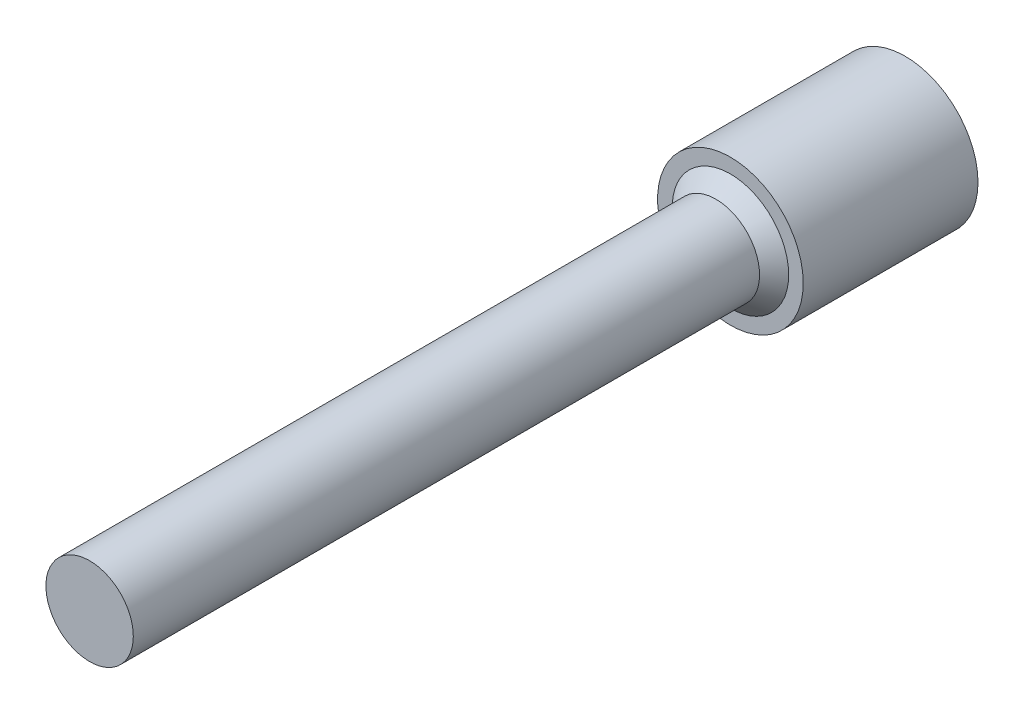
SolidWorks part; units mm, degrees
ref_plane "Front Plane" through (0, 0, 0) normal (0, 0, 1) x (1, 0, 0)
ref_plane "Top Plane" through (0, 0, 0) normal (0, 1, 0) x (1, 0, 0)
ref_plane "Right Plane" through (0, 0, 0) normal (1, 0, 0) x (0, 0, -1)
sketch "Sketch1" plane through (0, 0, 0) normal (0, 0, 1) x (1, 0, 0)
  circle A0 centre (0, 0) radius 2.5
  dimension "D1" = 5
extrude "Boss-Extrude1" add sketch "Sketch1" along normal blind 6
sketch "Sketch2" plane through (0, 0, 6) normal (0, 0, 1) x (1, 0, 0)
  circle A0 centre (0, 0) radius 1.5
  dimension "D1" = 3
extrude "Boss-Extrude2" add sketch "Sketch2" along normal blind 22
sketch "Sketch3" plane through (0, 0, 0) normal (0, 0, -1) x (-1, 0, 0)
  line L0 (0, 1) -> (0, -1) construction
  line L6 (0, 1) -> (-0.866, 0.5)
  line L7 (-0.866, 0.5) -> (-0.866, -0.5)
  line L8 (-0.866, -0.5) -> (0, -1)
  line L9 (0, -1) -> (0.866, -0.5)
  line L10 (0.866, -0.5) -> (0.866, 0.5)
  line L11 (0.866, 0.5) -> (0, 1)
  circle A0 centre (0, 0) radius 0.866 construction
  dimension "D1" = 1
extrude "Cut-Extrude1" cut sketch "Sketch3" against normal blind 1
chamfer "Chamfer1" distance 0.5 angle 45 1 edges at (1.5, 0, 6)
